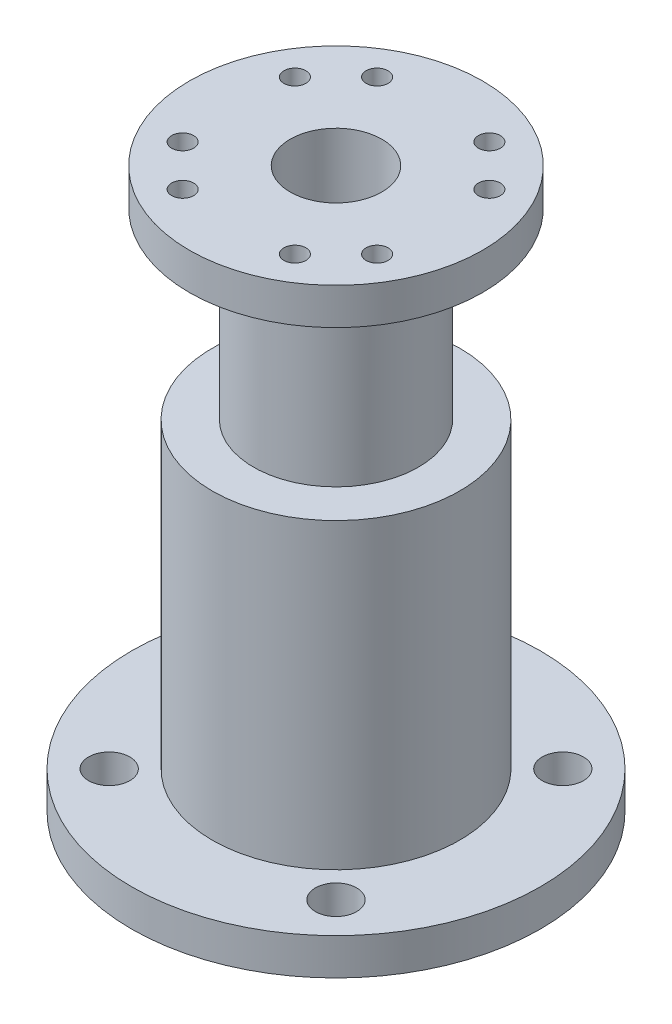
SolidWorks part; units mm, degrees
ref_plane "Front Plane" through (0, 0, 0) normal (0, 0, 1) x (1, 0, 0)
ref_plane "Top Plane" through (0, 0, 0) normal (0, 1, 0) x (1, 0, 0)
ref_plane "Right Plane" through (0, 0, 0) normal (1, 0, 0) x (0, 0, -1)
sketch "Sketch1" plane through (0, 0, 0) normal (0, 0, 1) x (1, 0, 0)
  line L0 (0, 0) -> (0, 69.1324) construction
  line L1 (9, 61) -> (9, 37)
  line L2 (9, 37) -> (13.5, 37)
  line L3 (13.5, 37) -> (13.5, 0)
  line L4 (5, 61) -> (9, 61)
  line L5 (9.5, 0) -> (13.5, 0)
  line L6 (5, 61) -> (5, 33)
  line L7 (5, 33) -> (9.5, 33)
  line L8 (9.5, 33) -> (9.5, 0)
  dimension "D2" = 28
  dimension "D3" = 33
  dimension "D4" = 9.5
  dimension "D5" = 5
  dimension "D1" = 4
revolve "Revolve1" add sketch "Sketch1" angle 360 about L0
sketch "Sketch2" plane through (0, 0, 0) normal (0, -1, 0) x (1, 0, 0)
  circle A0 centre (0, 0) radius 22.3
  circle A1 centre (0, 0) radius 13.5
  dimension "D1" = 44.6
extrude "Boss-Extrude1" add sketch "Sketch2" against normal blind 4
hole_wizard "M4 Clearance Hole1" positions "Sketch5" profile "Sketch4" hole size "M4" standard "ISO" end condition through all
sketch "Sketch5" plane through (0, 0, 0) normal (0, -1, 0) x (1, 0, 0)
  line L1 (12.3744, -12.3744) -> (-12.3744, -12.3744) construction
  line L2 (12.3744, -12.3744) -> (12.3744, 12.3744) construction
  line L3 (12.3744, 12.3744) -> (-12.3744, 12.3744) construction
  line L4 (-12.3744, -12.3744) -> (-12.3744, 12.3744) construction
  line L5 (12.3744, -12.3744) -> (-12.3744, 12.3744) construction
  line L6 (12.3744, 12.3744) -> (-12.3744, -12.3744) construction
  point P0 (-12.3744, 12.3744)
  point P96 (12.3744, 12.3744)
  point P102 (12.3744, -12.3744)
  point P104 (-12.3744, -12.3744)
  dimension "D2" = 35
sketch "Sketch4" plane through (-12.3744, 0, 12.3744) normal (1, 0, 0) x (0, 0, -1)
  line L0 (0, 0) -> (0, 61)
  line L1 (0, 61) -> (2.25, 61)
  line L2 (2.25, 61) -> (2.25, 0)
  line L5 (2.25, 0) -> (0, 0)
  line L11 (0, -6.35) -> (0, 107.95) construction
  dimension "Thru Hole Dia." = 4.5
  dimension "Thru Hole Depth" = 61
sketch "Sketch6" plane through (0, 61, 0) normal (0, 1, 0) x (1, 0, 0)
  circle A0 centre (0, 0) radius 9
  circle A1 centre (0, 0) radius 16
  circle A2 centre (0, 0) radius 9 construction
  dimension "D1" = 7
extrude "Boss-Extrude2" add sketch "Sketch6" against normal blind 4
hole_wizard "M2 Clearance Hole1" positions "Sketch8" profile "Sketch7" hole size "M2" standard "ISO" end condition up to next
sketch "Sketch8" plane through (0, 61, 0) normal (0, 1, 0) x (-1, 0, 0)
  line L0 (6.125, -10.6088) -> (-6.125, 10.6088) construction
  line L1 (6.125, 10.6088) -> (-6.125, -10.6088) construction
  line L3 (-10.6088, -6.125) -> (10.6088, 6.125) construction
  line L5 (10.6088, -6.125) -> (-10.6088, 6.125) construction
  line L7 (0, 0) -> (0, -8.4131) construction
  circle A0 centre (0, 0) radius 12.25 construction
  point P0 (10.6088, -6.125)
  point P1 (-10.6088, -6.125)
  point P3 (-6.125, 10.6088)
  point P5 (6.125, 10.6088)
  point P7 (10.6088, 6.125)
  point P9 (6.125, -10.6088)
  point P11 (-6.125, -10.6088)
  point P13 (-10.6088, 6.125)
  dimension "D1" = 24.5
  dimension "D2" = 60
  dimension "D3" = 60
  dimension "D4" = 30
  dimension "D5" = 30
sketch "Sketch7" plane through (-10.6088, 61, -6.125) normal (1, 0, 0) x (0, 0, 1)
  line L0 (0, 0) -> (0, 4)
  line L1 (0, 4) -> (1.2, 4)
  line L2 (1.2, 4) -> (1.2, 0)
  line L5 (1.2, 0) -> (0, 0)
  line L11 (0, -6.35) -> (0, 107.95) construction
  dimension "Thru Hole Dia." = 2.4
  dimension "Thru Hole Depth" = 4
equation "\"D3@Sketch8\" = \"D2@Sketch8\""
